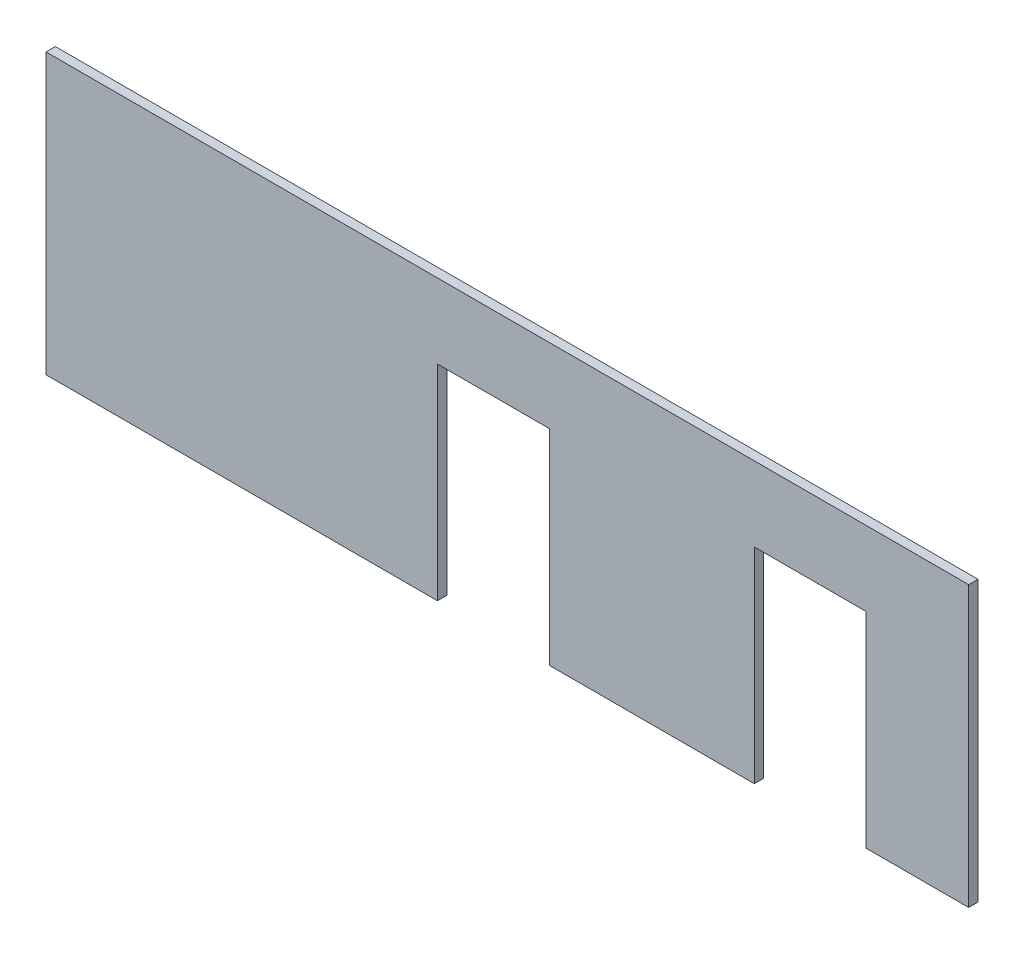
SolidWorks part; units mm, degrees
ref_plane "Front Plane" through (0, 0, 0) normal (0, 0, 1) x (1, 0, 0)
ref_plane "Top Plane" through (0, 0, 0) normal (0, 1, 0) x (1, 0, 0)
ref_plane "Right Plane" through (0, 0, 0) normal (1, 0, 0) x (0, 0, -1)
sketch "Sketch1" plane through (0, 0, 0) normal (0, 0, 1) x (1, 0, 0)
  line L0 (-77.5, 75) -> (-77.5, -75) construction
  line L1 (-247.5, 75) -> (247.5, 75)
  line L2 (-247.5, 75) -> (-247.5, -75)
  line L3 (-247.5, -75) -> (-37.5, -75)
  line L4 (247.5, 75) -> (247.5, -75)
  line L5 (-247.5, 75) -> (247.5, -75) construction
  line L6 (-247.5, -75) -> (247.5, 75) construction
  line L11 (192.5, -75) -> (192.5, 35)
  line L20 (77.5, 75) -> (77.5, -75) construction
  line L21 (22.5, -75) -> (22.5, 35)
  line L22 (132.5, 35) -> (132.5, -75)
  line L23 (132.5, 35) -> (192.5, 35)
  line L24 (192.5, -75) -> (247.5, -75)
  line L25 (22.5, 35) -> (-37.5, 35)
  line L26 (-37.5, 35) -> (-37.5, -75)
  line L27 (22.5, -75) -> (132.5, -75)
  point P0 (0, 0)
  point P15 (0, 0)
  point P16 (-7.5, 35)
  point P18 (162.5, 35)
  dimension "D1" = 495
  dimension "D2" = 150
  dimension "D3" = 170
  dimension "D4" = 170
  dimension "D5" = 110
  dimension "D6" = 60
  dimension "D7" = 70
  dimension "D8" = 60
  dimension "D9" = 85
  dimension "D10" = 110
extrude "Boss-Extrude1" add sketch "Sketch1" along normal blind 5
